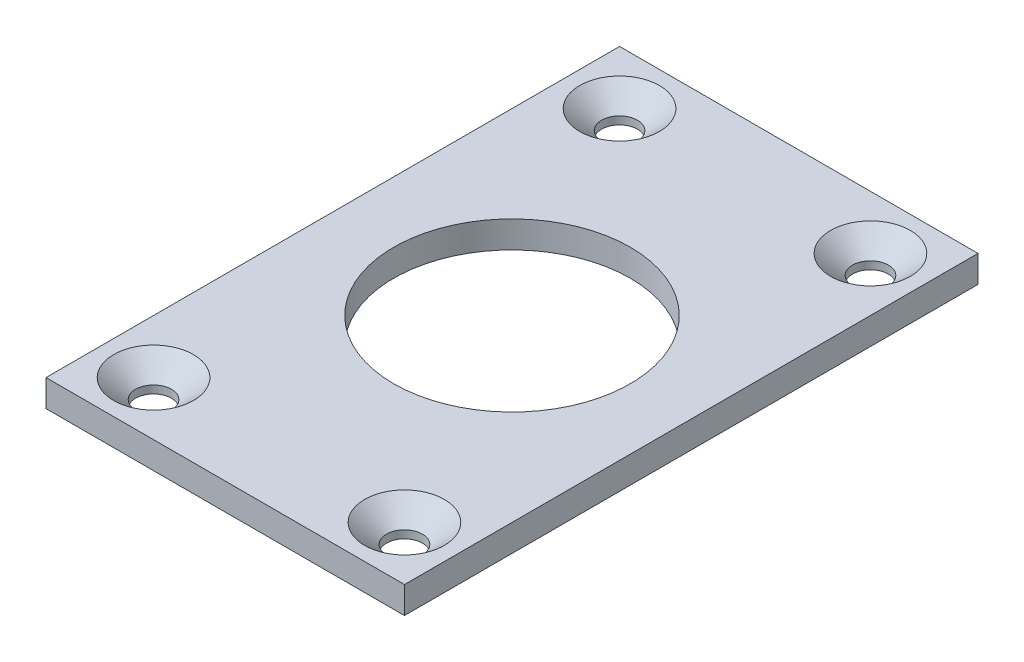
SolidWorks part; units mm, degrees
ref_plane "Front Plane" through (0, 0, 0) normal (0, 0, 1) x (1, 0, 0)
ref_plane "Top Plane" through (0, 0, 0) normal (0, 1, 0) x (1, 0, 0)
ref_plane "Right Plane" through (0, 0, 0) normal (1, 0, 0) x (0, 0, -1)
sketch "Sketch1" plane through (0, 0, 0) normal (0, 1, 0) x (1, 0, 0)
  line L0 (0, 50.8) -> (63.5, 50.8) construction
  line L1 (0, 0) -> (63.5, 0)
  line L2 (0, 0) -> (0, 101.6)
  line L3 (0, 101.6) -> (63.5, 101.6)
  line L4 (63.5, 0) -> (63.5, 101.6)
  line L5 (31.75, 101.6) -> (31.75, 0) construction
  circle A1 centre (31.75, 50.8) radius 20.955
  circle A2 centre (9.525, 92.075) radius 3.175
  circle A3 centre (53.975, 92.075) radius 3.175
  circle A4 centre (53.975, 9.525) radius 3.175
  circle A5 centre (9.525, 9.525) radius 3.175
  dimension "D3" = 9.525
  dimension "D1" = 63.5
  dimension "D2" = 101.6
  dimension "D4" = 9.525
extrude "Boss-Extrude1" add sketch "Sketch1" along normal blind 4.7625
chamfer "Chamfer1" distance 3.8862 angle 41 4 edges at (9.525, 4.7625, -88.9) (53.975, 4.7625, -6.35) (9.525, 4.7625, -12.7) (53.975, 4.7625, -95.25)
